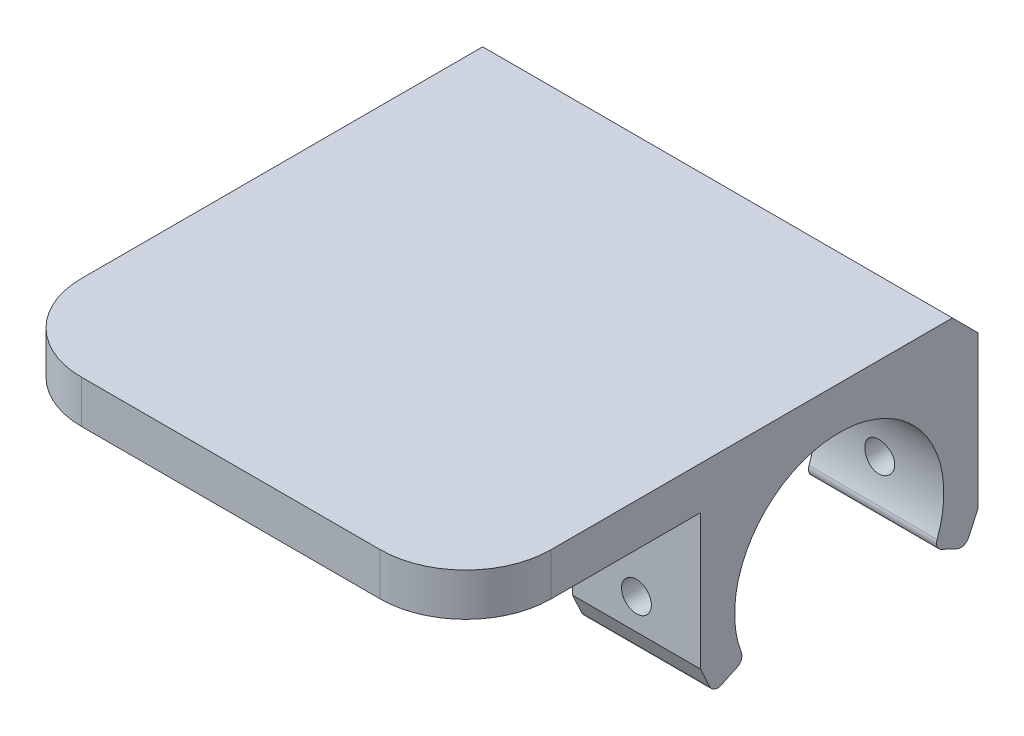
SolidWorks part; units mm, degrees
ref_plane "正面(Front)" through (0, 0, 0) normal (0, 0, 1) x (1, 0, 0)
ref_plane "平面(Top)" through (0, 0, 0) normal (0, 1, 0) x (1, 0, 0)
ref_plane "右側面(Right)" through (0, 0, 0) normal (1, 0, 0) x (0, 0, -1)
sketch "ｽｹｯﾁ1" plane through (0, 0, 0) normal (1, 0, 0) x (0, 0, -1)
  line L0 (16.25, 0) -> (16.25, 17.25)
  line L1 (16.25, 17.25) -> (-43.75, 17.25)
  line L2 (-43.75, 17.25) -> (-43.75, 12.25)
  line L3 (-43.75, 12.25) -> (-16.25, 12.25)
  line L4 (-16.25, 12.25) -> (-16.25, 0)
  circle A0 centre (0, 0) radius 12.25
  arc A1 (-16.25, 0) -> (16.25, 0) centre (0, 0) ccw
  point P3 (20.0566, 20.0566)
  dimension "D1" = 24.5
  dimension "D2" = 4
  dimension "D3" = 5
  dimension "D4" = 60
extrude "ﾎﾞｽ - 押し出し1" add sketch "ｽｹｯﾁ1" along normal mid plane 55
sketch "ｽｹｯﾁ3" plane through (27.5, 0, 0) normal (1, 0, 0) x (0, 0, -1)
  line L0 (-17.5578, -8.1873) -> (0, 0)
  line L1 (0, 0) -> (20.4014, -9.5133)
  line L2 (0, 0) -> (0, -23.8224) construction
  dimension "D1" = 65
extrude "ｶｯﾄ - 押し出し2" cut sketch "ｽｹｯﾁ3" along normal through all and the other way through all flip side to cut
sketch "ｽｹｯﾁ4" plane through (-27.5, 0, 0) normal (-1, 0, 0) x (0, 0, 1)
  line L0 (16.25, 0) -> (16.25, -3.6025)
  line L1 (16.25, -3.6025) -> (14.7275, -6.8675)
  line L2 (14.7275, -6.8675) -> (11.1023, -5.1771) construction
  line L3 (-16.25, 0) -> (-16.25, -3.6025)
  line L4 (-16.25, -3.6025) -> (-14.7275, -6.8675)
  line L5 (-11.1023, -5.1771) -> (-14.7275, -6.8675) construction
  arc A0 (14.7275, -6.8675) -> (16.25, 0) centre (0, 0) ccw construction
  arc A1 (14.7275, -6.8675) -> (16.25, 0) centre (0, 0) ccw
  arc A2 (-16.25, 0) -> (-14.7275, -6.8675) centre (0, 0) ccw construction
  arc A3 (-16.25, 0) -> (-14.7275, -6.8675) centre (0, 0) ccw
extrude "ﾎﾞｽ - 押し出し2" add sketch "ｽｹｯﾁ4" against normal up to surface (55 mm away) up to face at (27.5, 5.2171, 8.75)
fillet "ﾌｨﾚｯﾄ1" radius 1 4 edges at (0, -6.8675, 14.7275) (0, -5.1771, 11.1023) (0, -6.8675, -14.7275) (0, -5.1771, -11.1023)
sketch "ｽｹｯﾁ5" plane through (0, 0, -16.25) normal (0, 0, -1) x (-1, 0, 0)
  line L0 (0, 0) -> (0, 24.6204) construction
  circle A0 centre (20, 0) radius 1.75
  circle A1 centre (-20, 0) radius 1.75
  point P5 (0, 0)
  dimension "D1" = 3.5
  dimension "D2" = 40
extrude "ｶｯﾄ - 押し出し3" cut sketch "ｽｹｯﾁ5" against normal through all
sketch "ｽｹｯﾁ2" plane through (0, 0, 16.25) normal (0, 0, 1) x (1, 0, 0)
  line L0 (27.5, 12.25) -> (-27.5, 12.25) construction
  line L1 (12.5, 12.25) -> (-12.5, 12.25)
  line L2 (12.5, 12.25) -> (12.5, -17.75)
  line L3 (12.5, -17.75) -> (-12.5, -17.75)
  line L4 (-12.5, 12.25) -> (-12.5, -17.75)
  line L6 (0, 0) -> (0, 22.5292) construction
  point P6 (0, 0)
  point P7 (12.5, -17.4116)
  point P11 (0, 0)
  point P12 (0, 0)
  point P13 (0, 0)
  dimension "D1" = 25
  dimension "D2" = 30
extrude "ｶｯﾄ - 押し出し1" cut sketch "ｽｹｯﾁ2" against normal through all
fillet "ﾌｨﾚｯﾄ2" radius 10 2 edges at (-27.5, 14.75, 43.75) (27.5, 14.75, 43.75)
chamfer "面取り1" distance 3 angle 45 1 edges at (0, 17.25, -16.25)
